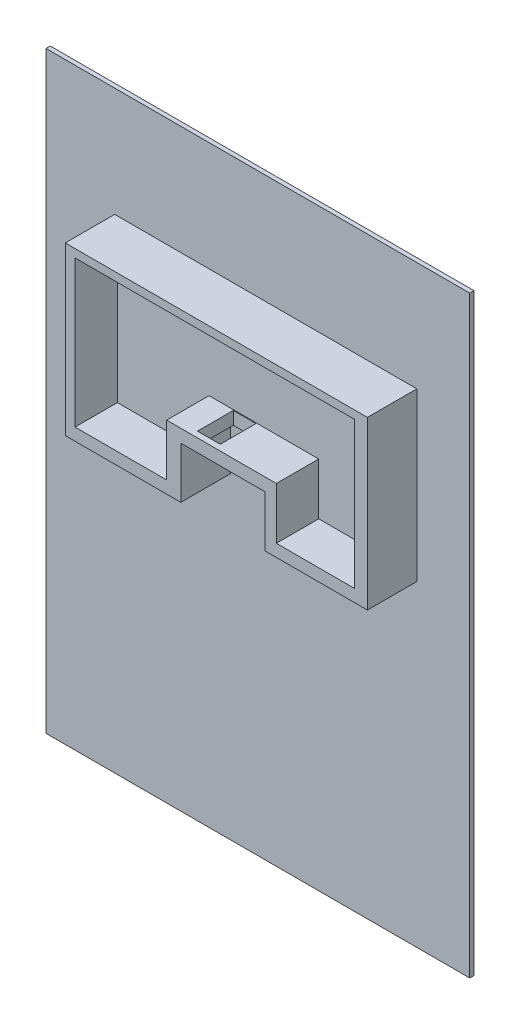
SolidWorks part; units mm, degrees
ref_plane "Ön Düzlem" through (0, 0, 0) normal (0, 0, 1) x (1, 0, 0)
ref_plane "Üst Düzlem" through (0, 0, 0) normal (0, 1, 0) x (1, 0, 0)
ref_plane "Sağ Düzlem" through (0, 0, 0) normal (1, 0, 0) x (0, 0, -1)
sketch "Çizim1" plane through (0, 0, 0) normal (0, 0, 1) x (1, 0, 0)
  line L1 (-13806.8007, 5017.1527) -> (16193.1993, 5017.1527)
  line L2 (-13806.8007, 5017.1527) -> (-13806.8007, -36982.8473)
  line L3 (-13806.8007, -36982.8473) -> (16193.1993, -36982.8473)
  line L4 (16193.1993, 5017.1527) -> (16193.1993, -36982.8473)
  dimension "D1" = 30000
  dimension "D2" = 42000
extrude "Yükseklik-Ekstrüzyon1" add sketch "Çizim1" along normal blind 300
sketch "Çizim2" plane through (0, 0, 0) normal (0, 0, 1) x (1, 0, 0)
  line L0 (-8945.804, -14541.0625) -> (-760.1866, -14541.0625)
  line L1 (-760.1866, -14541.0625) -> (-760.1866, -10913.3457)
  line L2 (-760.1866, -10913.3457) -> (5192.9896, -10913.3457)
  line L3 (5192.9896, -10913.3457) -> (5192.9896, -14541.0625)
  line L4 (5192.9896, -14541.0625) -> (12448.4232, -14541.0625)
  line L5 (12448.4232, -14541.0625) -> (12448.4232, -2727.7283)
  line L6 (12448.4232, -2727.7283) -> (-8945.804, -2727.7283)
  line L7 (-8945.804, -2727.7283) -> (-8945.804, -14541.0625)
extrude "Yükseklik-Ekstrüzyon2" add sketch "Çizim2" along normal blind 800
sketch "Çizim3" plane through (0, 0, 800) normal (0, 0, 1) x (1, 0, 0)
  line L0 (-8945.804, -2727.7283) -> (12448.4232, -2727.7283)
  line L1 (12448.4232, -2727.7283) -> (12448.4232, -14541.0625)
  line L2 (12448.4232, -14541.0625) -> (5192.9896, -14541.0625)
  line L3 (5192.9896, -14541.0625) -> (5192.9896, -10913.3457)
  line L4 (5192.9896, -10913.3457) -> (-760.1866, -10913.3457)
  line L5 (-760.1866, -10913.3457) -> (-760.1866, -14541.0625)
  line L6 (-760.1866, -14541.0625) -> (-8945.804, -14541.0625)
  line L7 (-8945.804, -14541.0625) -> (-8945.804, -2727.7283)
  line L8 (-8253.931, -3301.7856) -> (11531.5214, -3301.7856)
  line L9 (11531.5214, -3301.7856) -> (11531.5214, -13673.192)
  line L10 (11531.5214, -13673.192) -> (6000.1046, -13673.192)
  line L11 (6000.1046, -13673.192) -> (6000.1046, -10003.3097)
  line L12 (6000.1046, -10003.3097) -> (-1765.1536, -10003.3097)
  line L13 (-1765.1536, -10003.3097) -> (-1765.1536, -13673.192)
  line L14 (-1765.1536, -13673.192) -> (-8253.931, -13673.192)
  line L15 (-8253.931, -13673.192) -> (-8253.931, -3301.7856)
extrude "Yükseklik-Ekstrüzyon4" add sketch "Çizim3" along normal blind 3000
sketch "Çizim4" plane through (0, -10913.3457, 0) normal (0, -1, 0) x (1, 0, 0)
  line L1 (0, 3382.2167) -> (1609.7848, 3382.2167)
  line L2 (0, 3382.2167) -> (0, 848.1812)
  line L3 (0, 848.1812) -> (1609.7848, 848.1812)
  line L4 (1609.7848, 3382.2167) -> (1609.7848, 848.1812)
extrude "Kes-Ekstrüzyon1" cut sketch "Çizim4" against normal blind 2062
